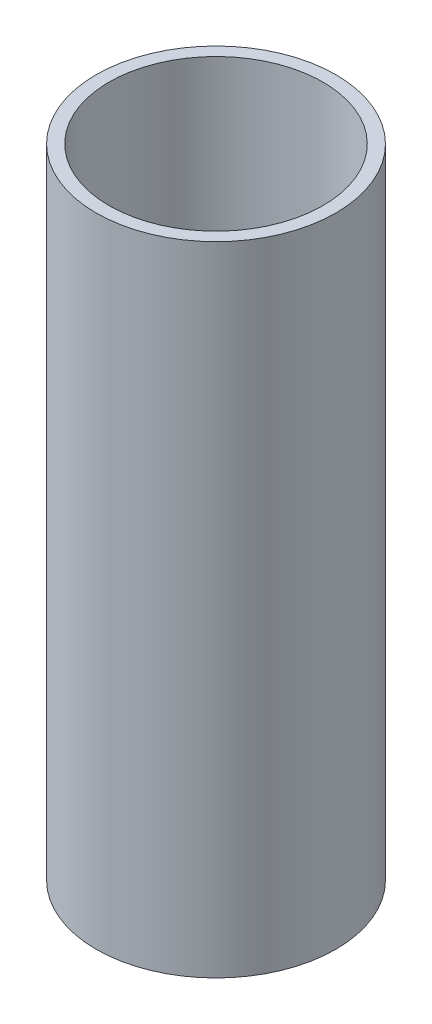
SolidWorks part; units mm, degrees
ref_plane "Front Plane" through (0, 0, 0) normal (0, 0, 1) x (1, 0, 0)
ref_plane "Top Plane" through (0, 0, 0) normal (0, 1, 0) x (1, 0, 0)
ref_plane "Right Plane" through (0, 0, 0) normal (1, 0, 0) x (0, 0, -1)
sketch "Sketch1" plane through (0, 0, 0) normal (0, 1, 0) x (1, 0, 0)
  circle A0 centre (0, 0) radius 14
  circle A1 centre (0, 0) radius 12.5
extrude "Boss-Extrude1" add sketch "Sketch1" along normal blind 74.498
scale "Scale2" scale about centroid uniform scaling yes scale factor 0.5
